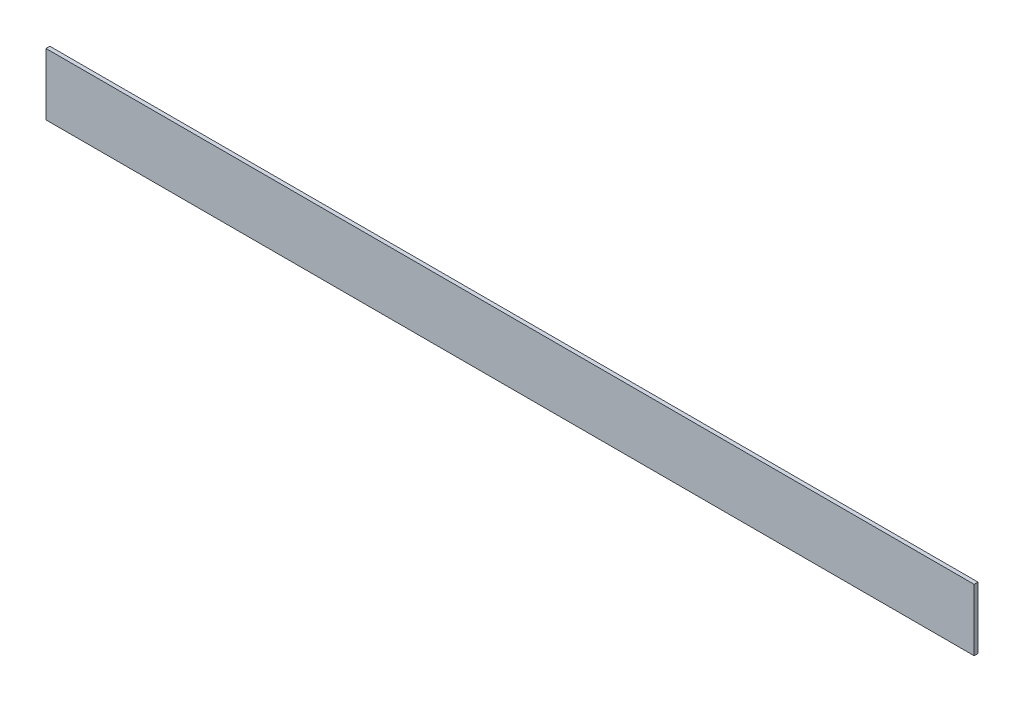
SolidWorks part; units mm, degrees
material "Nylon 6/10"
ref_plane "Front Plane" through (0, 0, 0) normal (0, 0, 1) x (1, 0, 0)
ref_plane "Top Plane" through (0, 0, 0) normal (0, 1, 0) x (1, 0, 0)
ref_plane "Right Plane" through (0, 0, 0) normal (1, 0, 0) x (0, 0, -1)
sketch "Sketch1" plane through (0, 0, 0) normal (0, 0, 1) x (1, 0, 0)
  line L6 (0, 0) -> (-762, 0)
  line L7 (0, 0) -> (0, -50.8)
  line L8 (0, -50.8) -> (-762, -50.8)
  line L9 (-762, 0) -> (-762, -50.8)
  dimension "D1" = 50.8
  dimension "D2" = 762
extrude "Boss-Extrude1" add sketch "Sketch1" along normal blind 3.175
